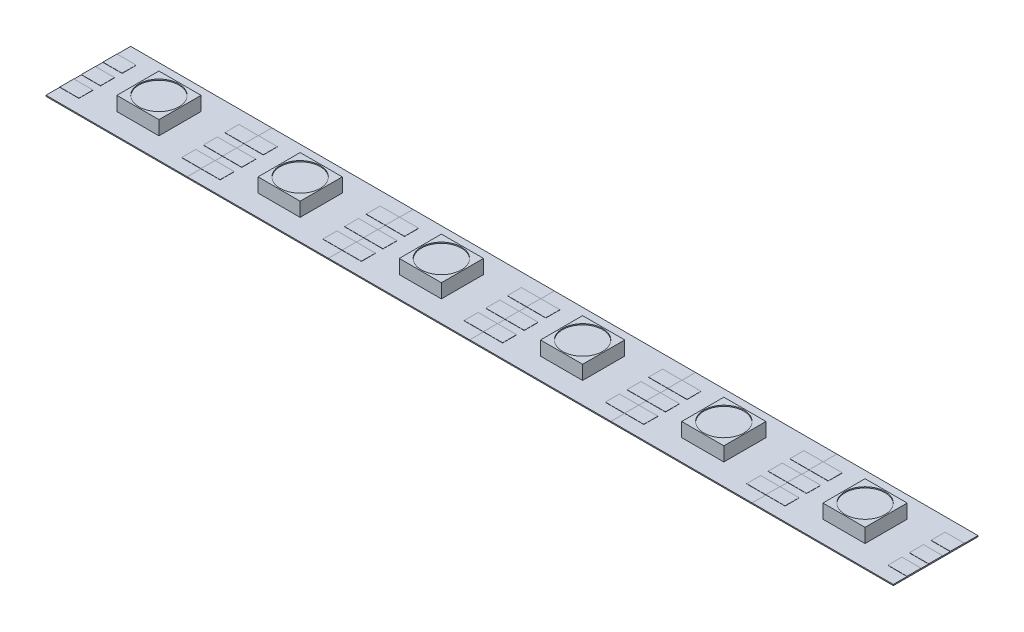
SolidWorks part; units mm, degrees
ref_plane "Front Plane" through (0, 0, 0) normal (0, 0, 1) x (1, 0, 0)
ref_plane "Top Plane" through (0, 0, 0) normal (0, 1, 0) x (1, 0, 0)
ref_plane "Right Plane" through (0, 0, 0) normal (1, 0, 0) x (0, 0, -1)
sketch "Sketch1" plane through (0, 0, 0) normal (0, 1, 0) x (1, 0, 0)
  line L0 (-8.3058, 4.9784) -> (8.3058, -4.9784) construction
  line L1 (-8.3058, 4.9784) -> (8.3058, 4.9784)
  line L2 (-8.3058, 4.9784) -> (-8.3058, -4.9784)
  line L3 (-8.3058, -4.9784) -> (8.3058, -4.9784)
  line L4 (8.3058, 4.9784) -> (8.3058, -4.9784)
  dimension "D1" = 9.9568
  dimension "D2" = 16.6116
extrude "Boss-Extrude1" add sketch "Sketch1" along normal blind 0.127
sketch "Sketch3" plane through (0, 0.127, 0) normal (0, 1, 0) x (1, 0, 0)
  line L0 (-8.3058, 4.9784) -> (8.3058, -4.9784) construction
  line L1 (-2.4765, 2.4765) -> (2.4765, -2.4765) construction
  line L2 (-2.4765, 2.4765) -> (2.4765, 2.4765)
  line L3 (-2.4765, 2.4765) -> (-2.4765, -2.4765)
  line L4 (-2.4765, -2.4765) -> (2.4765, -2.4765)
  line L5 (2.4765, 2.4765) -> (2.4765, -2.4765)
  dimension "D1" = 4.953
extrude "Boss-Extrude3" add sketch "Sketch3" along normal blind 1.651
sketch "Sketch4" plane through (0, 0.127, 0) normal (0, 1, 0) x (1, 0, 0)
  line L0 (-8.3058, 0) -> (8.3058, 0) construction
  line L1 (-8.3058, 4.9784) -> (-8.3058, -4.9784) construction
  line L2 (8.3058, -4.9784) -> (8.3058, 4.9784) construction
  line L3 (-6.047, 0) -> (-8.3058, 0) construction
  line L4 (-8.3058, 0.8255) -> (-6.047, 0.8255)
  line L5 (-8.3058, 0.8255) -> (-8.3058, -0.8255)
  line L6 (-8.3058, -0.8255) -> (-6.047, -0.8255)
  line L7 (-6.047, 0.8255) -> (-6.047, -0.8255)
  line L8 (-8.3058, 3.3655) -> (-6.047, 3.3655)
  line L9 (-6.047, 3.3655) -> (-6.047, 1.7145)
  line L10 (-8.3058, 1.7145) -> (-6.047, 1.7145)
  line L11 (-8.3058, 3.3655) -> (-8.3058, 1.7145)
  line L12 (-6.047, -3.3655) -> (-6.047, -1.7145)
  line L13 (-8.3058, -1.7145) -> (-6.047, -1.7145)
  line L14 (-8.3058, -3.3655) -> (-8.3058, -1.7145)
  line L15 (-8.3058, -3.3655) -> (-6.047, -3.3655)
  line L16 (0, 0) -> (0, -4.9784) construction
  line L17 (-8.3058, -4.9784) -> (8.3058, -4.9784) construction
  line L18 (8.3058, -3.3655) -> (8.3058, -1.7145)
  line L19 (8.3058, -3.3655) -> (6.047, -3.3655)
  line L20 (6.047, -3.3655) -> (6.047, -1.7145)
  line L21 (8.3058, -1.7145) -> (6.047, -1.7145)
  line L22 (8.3058, 0.8255) -> (8.3058, -0.8255)
  line L23 (8.3058, -0.8255) -> (6.047, -0.8255)
  line L24 (6.047, 0.8255) -> (6.047, -0.8255)
  line L25 (8.3058, 0.8255) -> (6.047, 0.8255)
  line L26 (8.3058, 1.7145) -> (6.047, 1.7145)
  line L27 (6.047, 3.3655) -> (6.047, 1.7145)
  line L28 (8.3058, 3.3655) -> (8.3058, 1.7145)
  line L29 (8.3058, 3.3655) -> (6.047, 3.3655)
  dimension "D1" = 1.651
  dimension "D2" = 2
extrude "Boss-Extrude4" add sketch "Sketch4" along normal blind 0.0254
sketch "Sketch5" plane through (0, 1.778, 0) normal (0, 1, 0) x (1, 0, 0)
  circle A0 centre (0, 0) radius 2.3483
extrude "Cut-Extrude1" cut sketch "Sketch5" against normal blind 0.127
pattern_linear "LPattern1" count 6 spacing 16.6116 along (1, 0, 0) of "Boss-Extrude3", "Boss-Extrude4", "Cut-Extrude1", "Boss-Extrude1"
